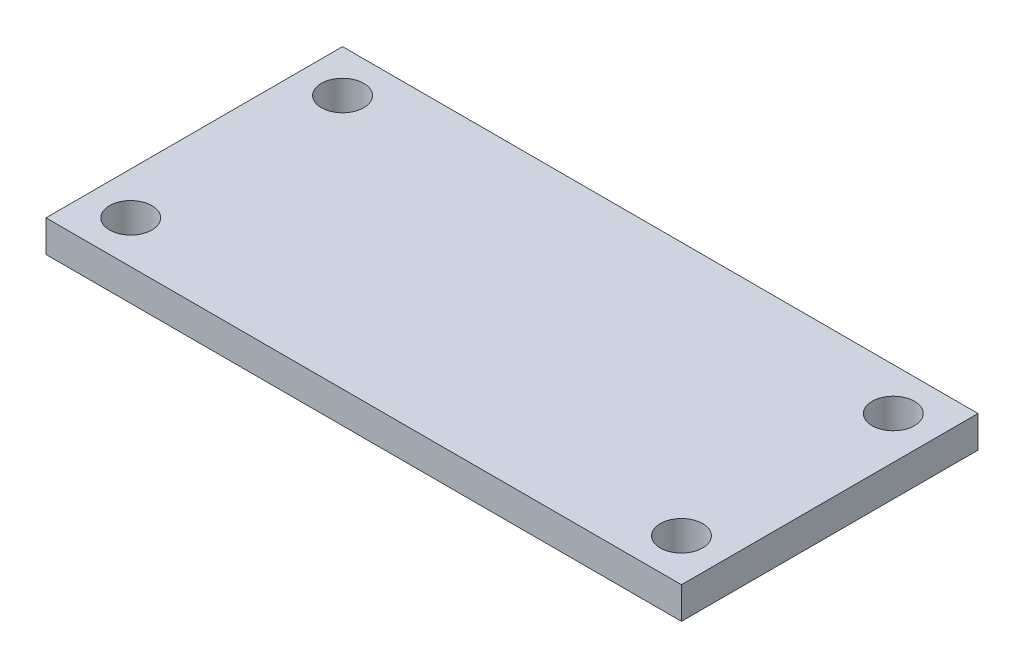
SolidWorks part; units mm, degrees
ref_plane "Front Plane" through (0, 0, 0) normal (0, 0, 1) x (1, 0, 0)
ref_plane "Top Plane" through (0, 0, 0) normal (0, 1, 0) x (1, 0, 0)
ref_plane "Right Plane" through (0, 0, 0) normal (1, 0, 0) x (0, 0, -1)
sketch "Sketch2" plane through (0, 0, 0) normal (0, 1, 0) x (1, 0, 0)
  line L1 (0, 0) -> (60, 0)
  line L2 (0, 0) -> (0, 28)
  line L3 (0, 28) -> (60, 28)
  line L4 (60, 0) -> (60, 28)
  dimension "D1" = 28
  dimension "D2" = 60
extrude "Boss-Extrude1" add sketch "Sketch2" along normal blind 3
sketch "Sketch3" plane through (0, 3, 0) normal (0, 1, 0) x (1, 0, 0)
  line L0 (0, 0) -> (60, 0) construction
  line L1 (0, 28) -> (0, 0) construction
  line L2 (60, 28) -> (0, 28) construction
  line L3 (60, 0) -> (60, 28) construction
  circle A0 centre (4, 4) radius 2
  circle A1 centre (4, 24) radius 2
  circle A2 centre (56, 24) radius 2
  circle A3 centre (56, 4) radius 2
  dimension "D3" = 4
  dimension "D6" = 4
  dimension "D9" = 4
  dimension "D12" = 4
  dimension "D1" = 4
  dimension "D2" = 4
  dimension "D4" = 4
  dimension "D5" = 4
  dimension "D7" = 4
  dimension "D8" = 4
  dimension "D10" = 4
  dimension "D11" = 4
extrude "Cut-Extrude1" cut sketch "Sketch3" against normal through all
